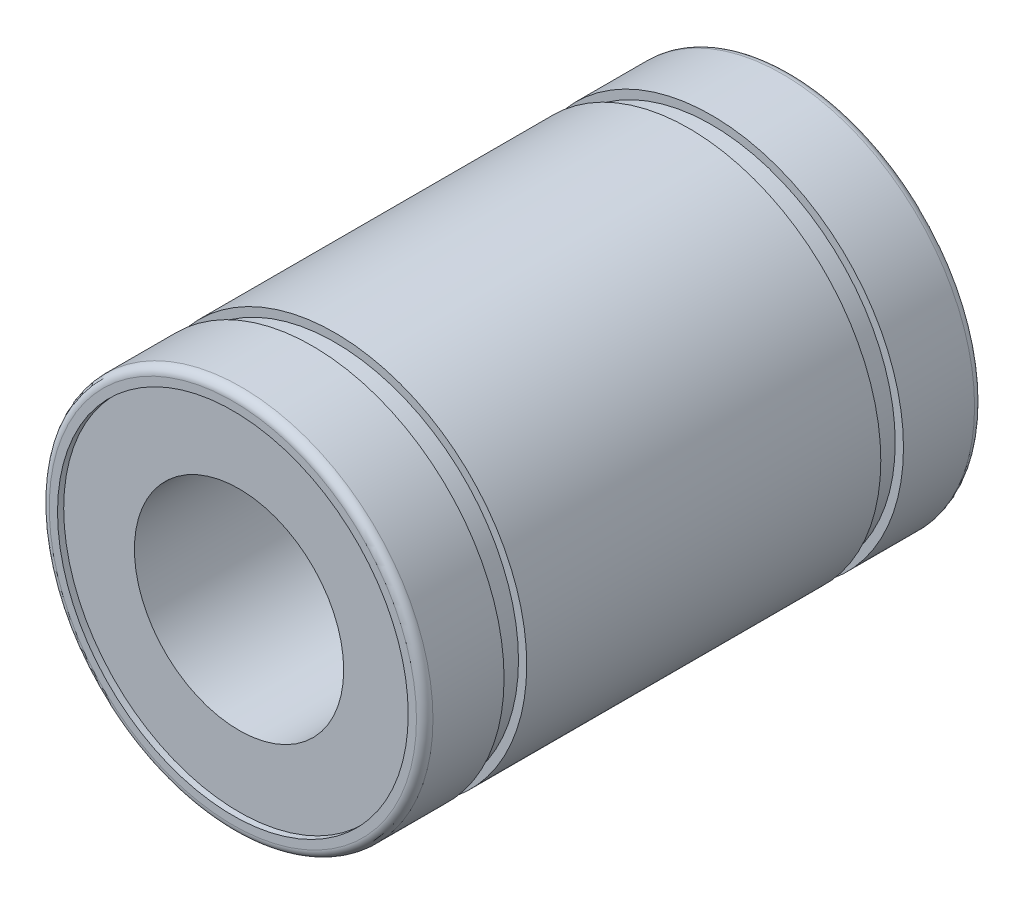
SolidWorks part; units mm, degrees
ref_plane "Front" through (0, 0, 0) normal (0, 0, 1) x (1, 0, 0)
ref_plane "Top" through (0, 0, 0) normal (0, 1, 0) x (1, 0, 0)
ref_plane "Right" through (0, 0, 0) normal (1, 0, 0) x (0, 0, -1)
sketch "Support-Right" plane through (0, 0, 0) normal (1, 0, 0) x (0, 0, -1)
  line L0 (-16, 0) -> (16, 0) construction
  line L1 (-15.6453, 6) -> (15.6453, 6)
  line L2 (15.6453, 6) -> (15.6453, 10.0537)
  line L3 (15.6453, 10.0537) -> (16, 10.0537)
  line L4 (16, 10.0537) -> (16, 10.5268)
  line L5 (15.5268, 11) -> (-15.5268, 11)
  line L6 (10.15, 11) -> (10.15, 10.5268)
  line L7 (-10.15, 11) -> (-10.15, 10.5268)
  line L8 (10.15, 10.5268) -> (11.45, 10.5268)
  line L9 (-10.15, 10.5268) -> (-11.45, 10.5268)
  line L10 (0, 0) -> (0, 11) construction
  line L11 (11.45, 10.5268) -> (11.45, 11)
  line L12 (-11.45, 10.5268) -> (-11.45, 11)
  line L13 (-15.6453, -6) -> (-15.6453, -10.0537)
  line L14 (-15.6453, -10.0537) -> (-16, -10.0537)
  line L15 (-16, 10.0537) -> (-16, 10.5268)
  line L16 (-15.6453, 10.0537) -> (-16, 10.0537)
  line L17 (-15.6453, 6) -> (-15.6453, 10.0537)
  line L18 (15.5268, 10.5268) -> (15.5268, 11) construction
  line L19 (-16, -10.0537) -> (-16, -10.5268)
  line L20 (-11.45, -10.5268) -> (-11.45, -11)
  line L21 (11.45, -10.5268) -> (11.45, -11)
  line L22 (-10.15, -10.5268) -> (-11.45, -10.5268)
  line L23 (10.15, -10.5268) -> (11.45, -10.5268)
  line L24 (-10.15, -11) -> (-10.15, -10.5268)
  line L25 (10.15, -11) -> (10.15, -10.5268)
  line L26 (15.5268, -11) -> (-15.5268, -11)
  line L27 (16, -10.0537) -> (16, -10.5268)
  line L28 (15.6453, -10.0537) -> (16, -10.0537)
  line L29 (15.6453, -6) -> (15.6453, -10.0537)
  line L30 (-15.6453, -6) -> (15.6453, -6)
  line L31 (15.6453, 6) -> (16, 10.0537) construction
  line L32 (10.15, 10.5268) -> (11.45, 11) construction
  arc A0 (16, 10.5268) -> (15.5268, 11) centre (15.5268, 10.5268) ccw
  arc A1 (-16, 10.5268) -> (-15.5268, 11) centre (-15.5268, 10.5268) cw
  arc A2 (-16, -10.5268) -> (-15.5268, -11) centre (-15.5268, -10.5268) ccw
  arc A3 (16, -10.5268) -> (15.5268, -11) centre (15.5268, -10.5268) cw
  dimension "D1" = 5
  dimension "Width-Track" = 1.3
  dimension "Dist-Track" = 22.9
  dimension "Diam-Shaft" = 12
  dimension "Length-Ball-Bearing" = 32
  dimension "Diam-Ball-Bearing" = 22
  dimension "D2" = 20
sketch "Sketch2" plane through (0, 0, 0) normal (1, 0, 0) x (0, 0, -1)
  line L0 (-15.6453, 10.0537) -> (-16, 10.0537) construction
  line L1 (15.6453, 10.0537) -> (16, 10.0537) construction
  line L2 (-16, 10.0537) -> (-16, 10.5268) construction
  line L3 (15.6453, 6) -> (15.6453, 10.0537) construction
  line L4 (16, 10.0537) -> (16, 10.5268) construction
  line L5 (15.5268, 11) -> (-15.5268, 11) construction
  line L6 (-15.6453, 6) -> (-15.6453, 10.0537) construction
  line L7 (-15.6453, 6) -> (15.6453, 6) construction
  line L8 (-16, 0) -> (16, 0) construction
  line L9 (-15.6453, 10.0537) -> (-16, 10.0537)
  line L10 (15.6453, 10.0537) -> (16, 10.0537)
  line L11 (-16, 10.0537) -> (-16, 10.5268)
  line L12 (15.6453, 6) -> (15.6453, 10.0537)
  line L13 (16, 10.0537) -> (16, 10.5268)
  line L14 (15.5268, 11) -> (-15.5268, 11)
  line L15 (-15.6453, 6) -> (-15.6453, 10.0537)
  line L16 (-15.6453, 6) -> (15.6453, 6)
  line L17 (-16, 0) -> (16, 0) construction
  arc A0 (-15.5268, 11) -> (-16, 10.5268) centre (-15.5268, 10.5268) ccw construction
  arc A1 (16, 10.5268) -> (15.5268, 11) centre (15.5268, 10.5268) ccw construction
  arc A2 (-15.5268, 11) -> (-16, 10.5268) centre (-15.5268, 10.5268) ccw
  arc A3 (16, 10.5268) -> (15.5268, 11) centre (15.5268, 10.5268) ccw
revolve "Body" add sketch "Sketch2" angle 360 about L17
sketch "Sketch3" plane through (0, 0, 0) normal (1, 0, 0) x (0, 0, -1)
  line L0 (11.45, 10.5268) -> (11.45, 11) construction
  line L1 (10.15, 10.5268) -> (11.45, 10.5268) construction
  line L2 (10.15, 11) -> (10.15, 10.5268) construction
  line L3 (-10.15, 11) -> (-10.15, 10.5268) construction
  line L4 (-10.15, 10.5268) -> (-11.45, 10.5268) construction
  line L5 (-11.45, 10.5268) -> (-11.45, 11) construction
  line L6 (-16, 0) -> (16, 0) construction
  line L7 (11.45, 10.5268) -> (11.45, 11)
  line L8 (10.15, 10.5268) -> (11.45, 10.5268)
  line L9 (10.15, 11) -> (10.15, 10.5268)
  line L10 (-10.15, 11) -> (-10.15, 10.5268)
  line L11 (-10.15, 10.5268) -> (-11.45, 10.5268)
  line L12 (-11.45, 10.5268) -> (-11.45, 11)
  line L13 (-16, 0) -> (16, 0) construction
  line L14 (-11.45, 11) -> (-10.15, 11)
  line L15 (10.15, 11) -> (11.45, 11)
revolve "Track" cut sketch "Sketch3" angle 360 about L13
sketch "Sketch4" plane through (0, 0, 0) normal (1, 0, 0) x (0, 0, -1)
  line L0 (10.15, 11) -> (10.15, 10.5268) construction
  line L1 (-10.15, 11) -> (-10.15, 10.5268) construction
  line L2 (10.15, 11) -> (10.15, 10.7634)
  line L3 (-10.15, 11) -> (-10.15, 10.7634)
  line L4 (-10.15, 10.7634) -> (10.15, 10.7634)
  line L5 (-10.15, 11) -> (10.15, 11)
  line L6 (-16, 0) -> (16, 0) construction
  line L7 (-16, 0) -> (16, 0) construction
revolve "Cosmetic-Cut" [suppressed] cut sketch "Sketch4" angle 20 about L7
pattern_circular "Pattern-Cosmetic-Cut" [suppressed] count 4 over 360 about axis through (0, 0, 16) along (0, 0, -1)
